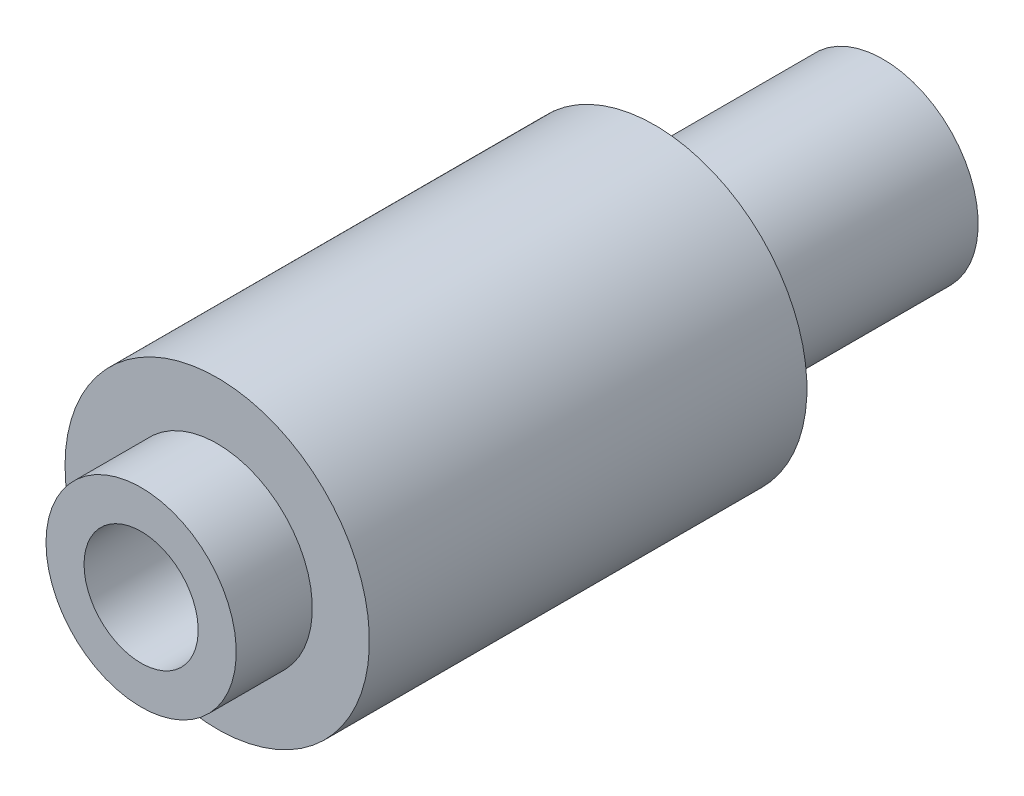
SolidWorks part; units mm, degrees
ref_plane "Front Plane" through (0, 0, 0) normal (0, 0, 1) x (1, 0, 0)
ref_plane "Top Plane" through (0, 0, 0) normal (0, 1, 0) x (1, 0, 0)
ref_plane "Right Plane" through (0, 0, 0) normal (1, 0, 0) x (0, 0, -1)
sketch "Sketch1" plane through (0, 0, 0) normal (0, 1, 0) x (1, 0, 0)
  line L0 (0, 28.5326) -> (0, -32.4457) construction
  line L1 (0, 9.75) -> (2.5, 9.75)
  line L2 (2.5, 9.75) -> (2.5, 3.75)
  line L3 (2.5, 3.75) -> (4, 3.75)
  line L4 (4, 3.75) -> (4, -7.75)
  line L5 (4, -7.75) -> (2.5, -7.75)
  line L6 (2.5, -7.75) -> (2.5, -9.75)
  line L7 (2.5, -9.75) -> (0, -9.75)
  line L8 (0, -9.75) -> (0, 9.75)
  point P5 (0, 0)
  dimension "D1" = 5
  dimension "D2" = 6
  dimension "D3" = 2
  dimension "D4" = 11.5
  dimension "D5" = 8
revolve "Revolve1" add sketch "Sketch1" angle 360 about L0
shell "Shell1" thickness 1
